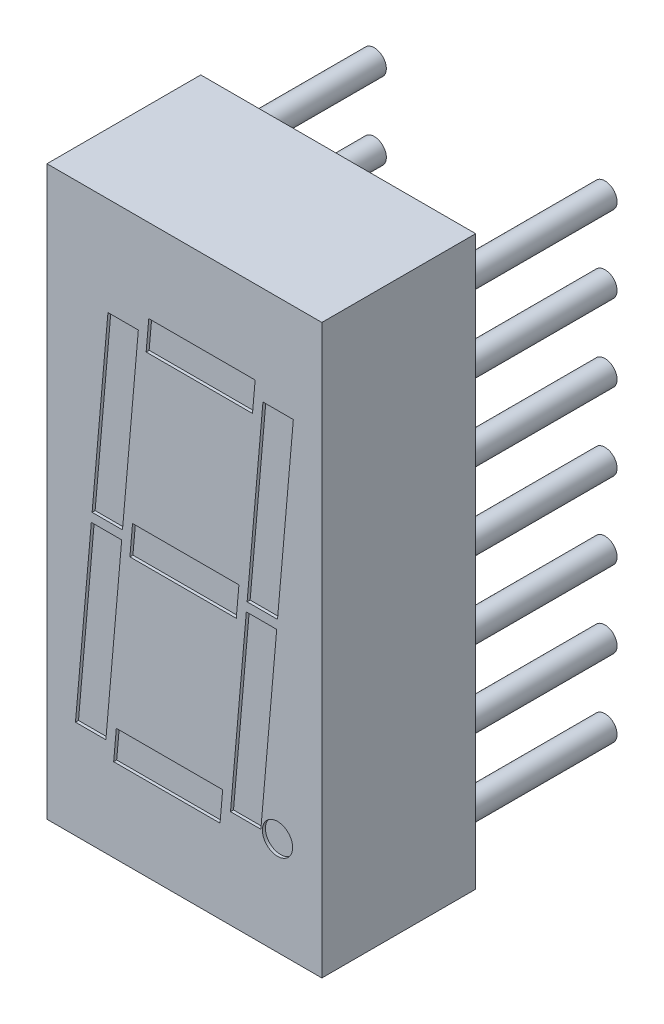
SolidWorks part; units mm, degrees
ref_plane "Front Plane" through (0, 0, 0) normal (0, 0, 1) x (1, 0, 0)
ref_plane "Top Plane" through (0, 0, 0) normal (0, 1, 0) x (1, 0, 0)
ref_plane "Right Plane" through (0, 0, 0) normal (1, 0, 0) x (0, 0, -1)
sketch "Sketch1" plane through (0, 0, 0) normal (0, 0, 1) x (1, 0, 0)
  line L0 (4.54, 9.375) -> (-4.54, 9.375)
  line L1 (4.54, 9.375) -> (4.54, -9.375)
  line L2 (-4.54, -9.375) -> (4.54, -9.375)
  line L3 (-4.54, -9.375) -> (-4.54, 9.375)
  line L4 (-4.54, 9.375) -> (4.54, -9.375) construction
  point P4 (0, 0)
  dimension "D1" = 9.08
  dimension "D2" = 18.75
extrude "Body" add sketch "Sketch1" along normal blind 5.08
sketch "Sketch2" plane through (0, 0, 0) normal (0, 0, -1) x (-1, 0, 0)
  line L0 (3.81, 0) -> (-3.81, 0) construction
  circle A0 centre (-3.81, 0) radius 0.4
  circle A1 centre (3.81, 0) radius 0.4
  point P4 (0, 0)
  dimension "D2" = 0.8
  dimension "D1" = 7.62
extrude "Pins" add sketch "Sketch2" along normal blind 5
pattern_linear "Pin Pattern 1" count 4 spacing 2.54 along (0, -1, 0) of "Pins"
pattern_linear "Pin Pattern 2" count 4 spacing 2.54 along (0, 1, 0) of "Pins"
sketch "Sketch3" plane through (0, 0, 5.08) normal (0, 0, 1) x (1, 0, 0)
  line L0 (-1.5218, 6.1272) -> (-2.0447, 0.15)
  line L1 (-1.5218, 6.1272) -> (-2.5256, 6.1272)
  line L2 (-2.5256, 6.1272) -> (-3.0485, 0.15)
  line L3 (-3.5977, -6.1272) -> (-2.5939, -6.1272)
  line L4 (2.5939, 6.1272) -> (2.071, 0.15)
  line L5 (1.5218, -6.1272) -> (2.5256, -6.1272)
  line L6 (2.5256, -6.1272) -> (3.0485, -0.15)
  line L7 (3.5977, 6.1272) -> (2.5939, 6.1272)
  line L8 (-1.7129, 0.5) -> (-1.8004, -0.5)
  line L9 (-1.7129, 0.5) -> (1.8004, 0.5)
  line L10 (1.8004, 0.5) -> (1.7129, -0.5)
  line L11 (1.7129, -0.5) -> (-1.8004, -0.5)
  line L12 (-1.2644, 5.6272) -> (-1.1769, 6.6272)
  line L13 (-1.1769, 6.6272) -> (2.3365, 6.6272)
  line L14 (2.3365, 6.6272) -> (2.249, 5.6272)
  line L15 (2.249, 5.6272) -> (-1.2644, 5.6272)
  line L16 (-2.249, -5.6272) -> (-2.3365, -6.6272)
  line L17 (-2.3365, -6.6272) -> (1.1769, -6.6272)
  line L18 (1.1769, -6.6272) -> (1.2644, -5.6272)
  line L19 (1.2644, -5.6272) -> (-2.249, -5.6272)
  line L20 (-3.0485, 0.15) -> (-2.0447, 0.15)
  line L21 (-3.0748, -0.15) -> (-2.071, -0.15)
  line L22 (2.071, 0.15) -> (3.0748, 0.15)
  line L23 (2.0447, -0.15) -> (3.0485, -0.15)
  line L24 (3.0748, 0.15) -> (3.5977, 6.1272)
  line L25 (2.0447, -0.15) -> (1.5218, -6.1272)
  line L26 (-3.0748, -0.15) -> (-3.5977, -6.1272)
  line L27 (-2.071, -0.15) -> (-2.5939, -6.1272)
  line L28 (-1.8004, -0.5) -> (1.8004, 0.5) construction
  line L29 (2.071, 0.15) -> (2.0447, -0.15) construction
  line L30 (1.7567, 0) -> (2.0578, 0) construction
  line L31 (-2.0447, 0.15) -> (-2.071, -0.15) construction
  line L32 (-1.7567, 0) -> (-2.0578, 0) construction
  line L33 (4.54, 9.375) -> (4.54, -9.375) construction
  circle A0 centre (3.0748, -6.1272) radius 0.5
  point P23 (0, 0)
  point P30 (2.0578, 0)
  point P32 (1.7567, 0)
  point P36 (-1.2206, 6.1272)
  point P37 (-2.2927, -6.1272)
  dimension "D6" = 1
  dimension "D1" = 1
  dimension "D2" = 3.5
  dimension "D3" = 5
  dimension "D4" = 6
  dimension "D5" = 0.3
extrude "LED Display" cut sketch "Sketch3" against normal blind 0.1
ref_plane "Board Surface" through (0, 0, -2) normal (0, 0, 1) x (1, 0, 0)
sketch "Component_Outline" plane through (0, 0, -2) normal (0, 0, 1) x (1, 0, 0)
  line L1 (4.54, 9.375) -> (-4.54, 9.375)
  line L2 (4.54, 9.375) -> (4.54, -9.375)
  line L3 (4.54, -9.375) -> (-4.54, -9.375)
  line L4 (-4.54, 9.375) -> (-4.54, -9.375)
  point P6 (0, 0)
